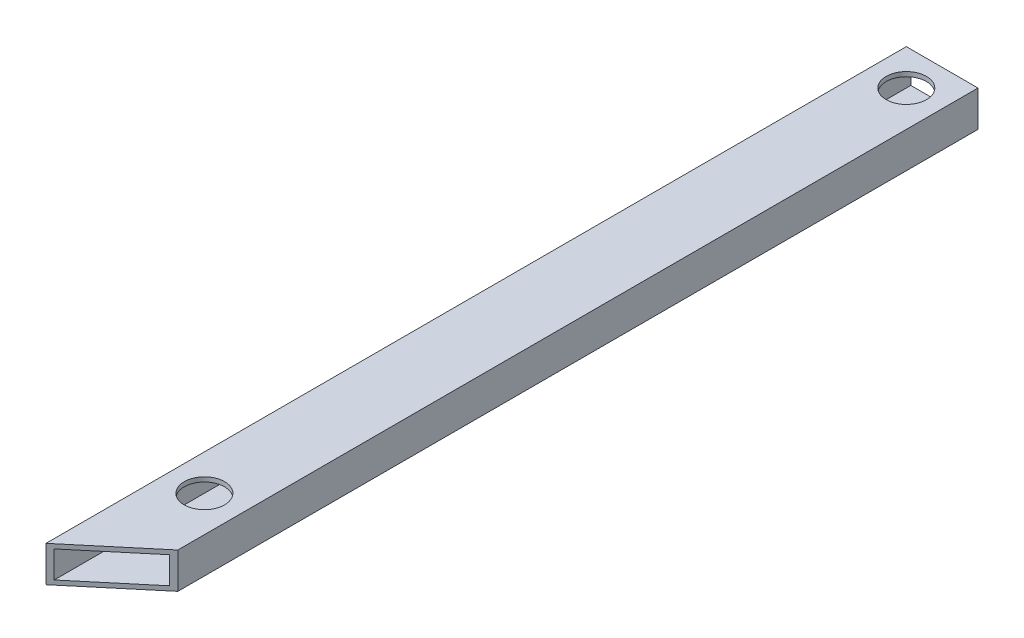
SolidWorks part; units mm, degrees
ref_plane "Front Plane" through (0, 0, 0) normal (0, 0, 1) x (1, 0, 0)
ref_plane "Top Plane" through (0, 0, 0) normal (0, 1, 0) x (1, 0, 0)
ref_plane "Right Plane" through (0, 0, 0) normal (1, 0, 0) x (0, 0, -1)
sketch "Sketch1" plane through (0, 0, 0) normal (0, 0, 1) x (1, 0, 0)
  line L1 (0, 0) -> (50.8, 0)
  line L2 (0, 0) -> (0, 25.4)
  line L3 (0, 25.4) -> (50.8, 25.4)
  line L4 (50.8, 0) -> (50.8, 25.4)
extrude "Boss-Extrude1" add sketch "Sketch1" along normal blind 609.6
sketch "Sketch2" plane through (0, 0, 0) normal (0, 0, -1) x (-1, 0, 0)
  line L1 (-3.175, 3.175) -> (-47.625, 3.175)
  line L2 (-3.175, 3.175) -> (-3.175, 22.225)
  line L3 (-3.175, 22.225) -> (-47.625, 22.225)
  line L4 (-47.625, 3.175) -> (-47.625, 22.225)
extrude "Cut-Extrude1" cut sketch "Sketch2" against normal blind 609.6
sketch "Sketch4" plane through (0, 0, 0) normal (0, -1, 0) x (1, 0, 0)
  line L9 (0, 609.6) -> (50.8, 566.9737)
  line L13 (50.8, 609.6) -> (50.8, 0) construction
  line L14 (50.8, 566.9737) -> (50.8, 609.6)
  line L15 (50.8, 609.6) -> (0, 609.6)
  dimension "D1" = 50
extrude "Cut-Extrude3" cut sketch "Sketch4" against normal blind 25.4
sketch "Sketch6" plane through (0, 25.4, 0) normal (0, 1, 0) x (1, 0, 0)
  line L0 (25.4, 0) -> (25.4, -25.4) construction
  line L1 (50.8, 0) -> (0, 0) construction
  circle A0 centre (25.4, -25.4) radius 14.2875
extrude "Cut-Extrude5" cut sketch "Sketch6" against normal blind 3.175
sketch "Sketch8" plane through (0, 25.4, 0) normal (0, 1, 0) x (1, 0, 0)
  circle A0 centre (25.4, -522.7626) radius 14.2875
extrude "Cut-Extrude7" cut sketch "Sketch8" against normal blind 3.175
